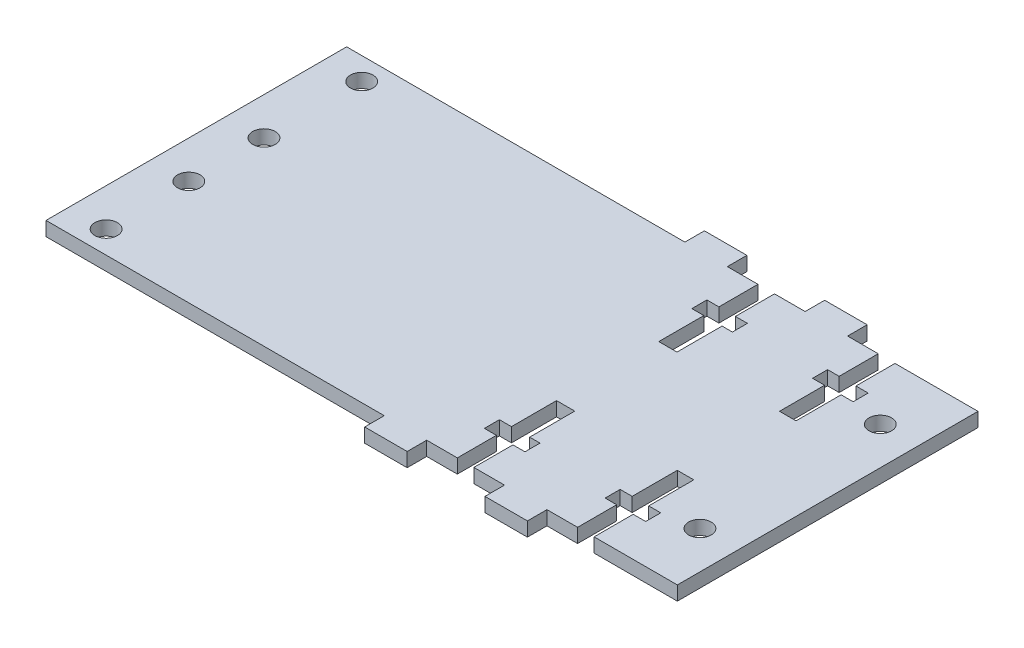
SolidWorks part; units mm, degrees
ref_plane "Front Plane" through (0, 0, 0) normal (0, 0, 1) x (1, 0, 0)
ref_plane "Top Plane" through (0, 0, 0) normal (0, 1, 0) x (1, 0, 0)
ref_plane "Right Plane" through (0, 0, 0) normal (1, 0, 0) x (0, 0, -1)
sketch "Sketch1" plane through (0, 0, 0) normal (0, 1, 0) x (1, 0, 0)
  line L3 (107.95, 0) -> (107.95, 38.1)
  line L6 (107.95, -12.7) -> (107.95, 0)
  line L7 (6.35, 38.1) -> (6.35, -12.7)
  line L8 (6.35, -12.7) -> (25.4, -12.7)
  line L9 (25.4, -12.7) -> (25.4, -16.002)
  line L10 (25.4, -16.002) -> (32.5755, -16.002)
  line L11 (32.5755, -16.002) -> (32.5755, -12.7)
  line L13 (37.7507, -3.556) -> (37.7507, 4.064)
  line L15 (32.5755, -12.7) -> (37.7507, -12.7)
  line L16 (37.7507, -12.7) -> (37.7507, -6.096)
  line L17 (37.7507, -6.096) -> (35.7188, -6.096)
  line L18 (35.7188, -6.096) -> (35.7188, -3.556)
  line L19 (35.7188, -3.556) -> (37.7507, -3.556)
  line L20 (40.5448, -12.7) -> (40.5448, -6.096)
  line L21 (40.5448, -6.096) -> (42.5768, -6.096)
  line L22 (42.5768, -6.096) -> (42.5768, -3.556)
  line L23 (42.5768, -3.556) -> (40.8287, -3.556)
  line L24 (40.8287, -3.556) -> (40.8287, 4.064)
  line L25 (37.7507, 4.064) -> (40.8287, 4.064)
  line L27 (40.5448, -12.7) -> (45.72, -12.7)
  line L28 (58.1517, 4.064) -> (60.9457, 4.064)
  line L31 (60.9457, 4.064) -> (60.9457, -3.556)
  line L32 (45.72, -12.7) -> (45.72, -16.002)
  line L33 (45.72, -16.002) -> (52.8955, -16.002)
  line L34 (52.8955, -16.002) -> (52.8955, -12.7)
  line L37 (52.8955, -12.7) -> (58.0708, -12.7)
  line L38 (58.0708, -12.7) -> (58.0708, -6.096)
  line L39 (58.0708, -6.096) -> (56.1197, -6.096)
  line L40 (56.1197, -6.096) -> (56.1197, -3.556)
  line L41 (56.1197, -3.556) -> (58.1517, -3.556)
  line L42 (58.1517, -3.556) -> (58.1517, 4.064)
  line L43 (60.9457, -3.556) -> (62.9777, -3.556)
  line L44 (62.9777, -3.556) -> (62.9777, -6.096)
  line L45 (62.9777, -6.096) -> (60.8648, -6.096)
  line L46 (60.8648, -6.096) -> (60.8648, -12.7)
  line L49 (45.72, 41.402) -> (52.8955, 41.402)
  line L50 (52.8955, 41.402) -> (52.8955, 38.1)
  line L51 (52.8955, 38.1) -> (58.0707, 38.1)
  line L52 (40.5447, 38.1) -> (45.72, 38.1)
  line L53 (45.72, 38.1) -> (45.72, 41.402)
  line L54 (25.4, 38.1) -> (25.4, 41.402)
  line L55 (32.5755, 38.1) -> (37.7507, 38.1)
  line L56 (32.5755, 41.402) -> (32.5755, 38.1)
  line L57 (25.4, 41.402) -> (32.5755, 41.402)
  line L58 (42.5767, 31.496) -> (42.5767, 28.956)
  line L59 (40.5447, 31.496) -> (42.5767, 31.496)
  line L60 (40.5447, 38.1) -> (40.5447, 31.496)
  line L61 (35.7187, 31.496) -> (35.7187, 28.956)
  line L62 (37.7507, 31.496) -> (35.7187, 31.496)
  line L63 (37.7507, 38.1) -> (37.7507, 31.496)
  line L64 (60.9056, 31.496) -> (60.9056, 38.1)
  line L65 (62.9777, 31.496) -> (60.9056, 31.496)
  line L66 (62.9777, 28.956) -> (62.9777, 31.496)
  line L67 (56.1197, 31.496) -> (56.1197, 28.956)
  line L68 (58.0707, 31.496) -> (56.1197, 31.496)
  line L69 (58.0707, 38.1) -> (58.0707, 31.496)
  line L70 (60.9457, 28.956) -> (62.9777, 28.956)
  line L71 (58.1517, 28.956) -> (58.1517, 21.336)
  line L72 (56.1197, 28.956) -> (58.1517, 28.956)
  line L73 (60.9457, 21.336) -> (60.9457, 28.956)
  line L74 (58.1517, 21.336) -> (60.9457, 21.336)
  line L75 (37.7507, 21.336) -> (40.8287, 21.336)
  line L76 (40.8287, 28.956) -> (40.8287, 21.336)
  line L77 (42.5767, 28.956) -> (40.8287, 28.956)
  line L78 (35.7187, 28.956) -> (37.7507, 28.956)
  line L79 (37.7507, 28.956) -> (37.7507, 21.336)
  line L80 (6.35, 38.1) -> (25.4, 38.1)
  line L81 (60.9056, 38.1) -> (107.95, 38.1)
  line L82 (60.8648, -12.7) -> (66.04, -12.7)
  line L87 (78.0358, -12.7) -> (80.8298, -12.7)
  line L91 (66.04, -12.7) -> (73.2155, -12.7)
  line L92 (32.5755, -16.002) -> (39.1478, -16.002)
  line L95 (73.2155, -12.7) -> (78.0358, -12.7)
  line L104 (80.8298, -12.7) -> (107.95, -12.7)
  dimension "D1" = 50.8
  dimension "D2" = 19.05
  dimension "D3" = 3.302
  dimension "D4" = 7.1755
  dimension "D5" = 6.858
  dimension "D6" = 7.1755
  dimension "D7" = 6.604
  dimension "D8" = 2.032
  dimension "D9" = 2.54
  dimension "D10" = 7.62
  dimension "D11" = 2.032
  dimension "D12" = 2.54
  dimension "D13" = 2.032
  dimension "D14" = 2.794
  dimension "D15" = 2.54
  dimension "D16" = 6.858
  dimension "D17" = 2.032
  dimension "D18" = 2.032
  dimension "D19" = 101.6
  dimension "D22" = 6.5723
  dimension "D27" = 2.794
extrude "Boss-Extrude1" add sketch "Sketch1" along normal blind 2.3813
ref_plane "Plane1" through (0, 0, -12.7) normal (0, 0, -1) x (-1, 0, 0)
sketch "Sketch3" plane through (0, 2.3813, 0) normal (0, 1, 0) x (1, 0, 0)
  line L0 (6.35, 38.1) -> (-31.75, 38.1)
  line L1 (-31.75, 38.1) -> (-31.75, -12.7)
  line L2 (-31.75, -12.7) -> (6.35, -12.7)
  line L3 (6.35, -12.7) -> (6.35, 38.1)
  line L4 (55.88, 12.7) -> (-55.88, 12.7) construction
  line L9 (-25.4, -8.89) -> (-31.75, -8.89)
  circle A4 centre (-25.4, -8.89) radius 1.905
  circle A5 centre (-25.4, 5.08) radius 1.905
  circle A6 centre (-25.4, 17.78) radius 1.905
  circle A7 centre (-25.4, 34.29) radius 1.905
  dimension "D3" = 5.08
  dimension "D4" = 6.35
  dimension "D6" = 3.81
  dimension "D7" = 3.81
  dimension "D1" = 38.1
  dimension "D2" = 13.97
  dimension "D8" = 12.7
  dimension "D9" = 16.51
extrude "Boss-Extrude4" add sketch "Sketch3" against normal blind 2.3813
sketch "Sketch5" plane through (0, 2.3813, 0) normal (0, 1, 0) x (1, 0, 0)
sketch "Sketch7" plane through (0, 2.3813, 0) normal (0, 1, 0) x (1, 0, 0)
  line L0 (107.95, -12.7) -> (74.93, -12.7)
  line L1 (60.8648, -12.7) -> (107.95, -12.7) construction
  line L2 (74.93, -12.7) -> (74.93, 38.1)
  line L3 (60.9056, 38.1) -> (107.95, 38.1) construction
  line L4 (74.93, 38.1) -> (107.95, 38.1)
  line L5 (107.95, 38.1) -> (107.95, -12.7)
  dimension "65" = 33.02
extrude "Cut-Extrude3" cut sketch "Sketch7" against normal through all
sketch "Sketch8" plane through (0, 2.3813, 0) normal (0, 1, 0) x (1, 0, 0)
  line L0 (74.93, 12.7) -> (74.93, -2.54)
  line L1 (74.93, 12.7) -> (74.93, 27.94)
  line L2 (74.93, 38.1) -> (74.93, -12.7) construction
  line L3 (74.93, 27.94) -> (68.58, 27.94)
  line L4 (74.93, -2.54) -> (68.58, -2.54)
  circle A0 centre (68.58, -2.54) radius 1.905
  circle A1 centre (68.58, 27.94) radius 1.905
  dimension "D4" = 3.81
  dimension "D5" = 3.81
  dimension "D1" = 15.24
  dimension "D2" = 15.24
  dimension "D3" = 6.35
extrude "Cut-Extrude4" cut sketch "Sketch8" against normal through all
